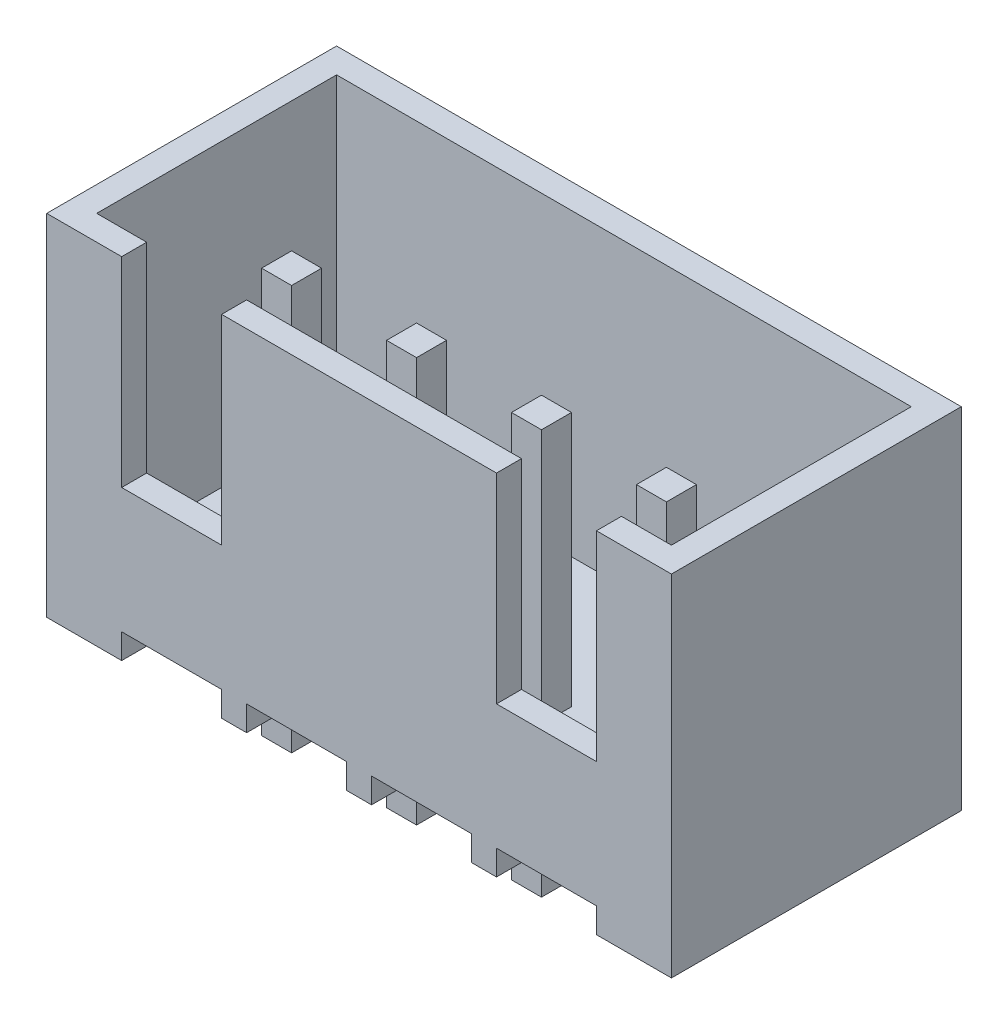
SolidWorks part; units mm, degrees
ref_plane "前视基准面" through (0, 0, 0) normal (0, 0, 1) x (1, 0, 0)
ref_plane "上视基准面" through (0, 0, 0) normal (0, 1, 0) x (1, 0, 0)
ref_plane "右视基准面" through (0, 0, 0) normal (1, 0, 0) x (0, 0, -1)
sketch "草图1" plane through (0, 0, 0) normal (0, 0, 1) x (1, 0, 0)
  line L0 (4, 0) -> (4, 0.5)
  line L1 (0, 0) -> (1.5, 0)
  line L2 (0, 0) -> (0, 7)
  line L3 (0, 7) -> (12.5, 7)
  line L4 (12.5, 0) -> (12.5, 7)
  line L5 (4, 0.5) -> (6, 0.5)
  line L6 (6, 0.5) -> (6, 0)
  line L7 (6.5, 0) -> (6.5, 0.5)
  line L8 (6.5, 0.5) -> (8.5, 0.5)
  line L9 (8.5, 0.5) -> (8.5, 0)
  line L10 (6, 0) -> (6.5, 0)
  line L11 (8.5, 0) -> (9, 0)
  line L12 (6.25, 4.6706) -> (6.25, 50004.6706) construction
  line L13 (3.75, 3.7509) -> (3.75, 50003.7509) construction
  line L14 (1.5, 0.5) -> (1.5, 0)
  line L15 (3.5, 0) -> (3.5, 0.5)
  line L16 (3.5, 0.5) -> (1.5, 0.5)
  line L17 (9, 0) -> (9, 0.5)
  line L18 (9, 0.5) -> (11, 0.5)
  line L19 (11, 0.5) -> (11, 0)
  line L20 (11, 0) -> (12.5, 0)
  line L21 (3.5, 0) -> (4, 0)
  dimension "D1" = 12.5
  dimension "D2" = 7
  dimension "D3" = 2.5
  dimension "D4" = 0.5
  dimension "D5" = 0.5
  dimension "D6" = 4
  dimension "D7" = 2.5
extrude "凸台-拉伸1" add sketch "草图1" along normal blind 5.8
sketch "草图2" plane through (0, 7, 0) normal (0, 1, 0) x (1, 0, 0)
  line L0 (0, -5.8) -> (0, 0) construction
  line L1 (0.5, -0.5) -> (12, -0.5)
  line L2 (0.5, -0.5) -> (0.5, -5.3)
  line L3 (0.5, -5.3) -> (12, -5.3)
  line L4 (12, -0.5) -> (12, -5.3)
  line L5 (12.5, 0) -> (0, 0) construction
  line L6 (12.5, -5.8) -> (12.5, 0) construction
  line L7 (12.5, -5.8) -> (0, -5.8) construction
  dimension "D1" = 0.5
  dimension "D2" = 0.5
  dimension "D3" = 0.5
  dimension "D4" = 0.5
extrude "切除-拉伸1" cut sketch "草图2" against normal blind 6
sketch "草图3" plane through (0, 0, 0) normal (0, -1, 0) x (1, 0, 0)
  line L0 (4, 0) -> (6, 0) construction
  line L1 (4.7, 3.7) -> (5.3, 3.7)
  line L2 (4.7, 3.7) -> (4.7, 3.1)
  line L3 (4.7, 3.1) -> (5.3, 3.1)
  line L4 (5.3, 3.7) -> (5.3, 3.1)
  line L5 (5, 4.7075) -> (5, 50004.7075) construction
  line L6 (4, 5.8) -> (4, 0) construction
  line L7 (6, 5.8) -> (6, 0) construction
  line L8 (6.25, 2.7254) -> (6.25, 50002.7254) construction
  line L9 (0, 5.8) -> (0, 0) construction
  line L10 (12.5, 5.8) -> (12.5, 0) construction
  line L11 (7.2, 3.7) -> (7.2, 3.1)
  line L12 (7.8, 3.1) -> (7.2, 3.1)
  line L13 (7.8, 3.7) -> (7.8, 3.1)
  line L14 (7.8, 3.7) -> (7.2, 3.7)
  line L15 (3.75, 0.9249) -> (3.75, -49999.0751) construction
  line L16 (2.8, 3.7) -> (2.8, 3.1)
  line L17 (2.2, 3.7) -> (2.2, 3.1)
  line L18 (2.8, 3.1) -> (2.2, 3.1)
  line L19 (2.8, 3.7) -> (2.2, 3.7)
  line L20 (9.7, 3.7) -> (9.7, 3.1)
  line L21 (9.7, 3.1) -> (10.3, 3.1)
  line L22 (10.3, 3.7) -> (10.3, 3.1)
  line L23 (9.7, 3.7) -> (10.3, 3.7)
  dimension "D1" = 0.6
  dimension "D2" = 3.1
  dimension "D3" = 2.5
  dimension "D4" = 2.5
extrude "凸台-拉伸2" add sketch "草图3" against normal blind 6.1 and the other way blind 2
sketch "草图5" plane through (0, 0, 5.8) normal (0, 0, 1) x (1, 0, 0)
  line L0 (0, 7) -> (0, 0) construction
  line L2 (1.5, 7) -> (1.5, 3)
  line L3 (12.5, 7) -> (0, 7) construction
  line L4 (1.5, 3) -> (3.5, 3)
  line L5 (11, 3) -> (11, 7)
  line L6 (1.5, 7) -> (3.5, 7)
  line L7 (12.5, 0) -> (12.5, 7) construction
  line L8 (3.5, 7) -> (3.5, 3)
  line L9 (9, 7) -> (9, 3)
  line L10 (9, 7) -> (11, 7)
  line L11 (9, 3) -> (11, 3)
  dimension "D1" = 1.5
  dimension "D2" = 1.5
  dimension "D3" = 4
  dimension "D4" = 2
  dimension "D5" = 2
extrude "切除-拉伸2" cut sketch "草图5" against normal blind 1
